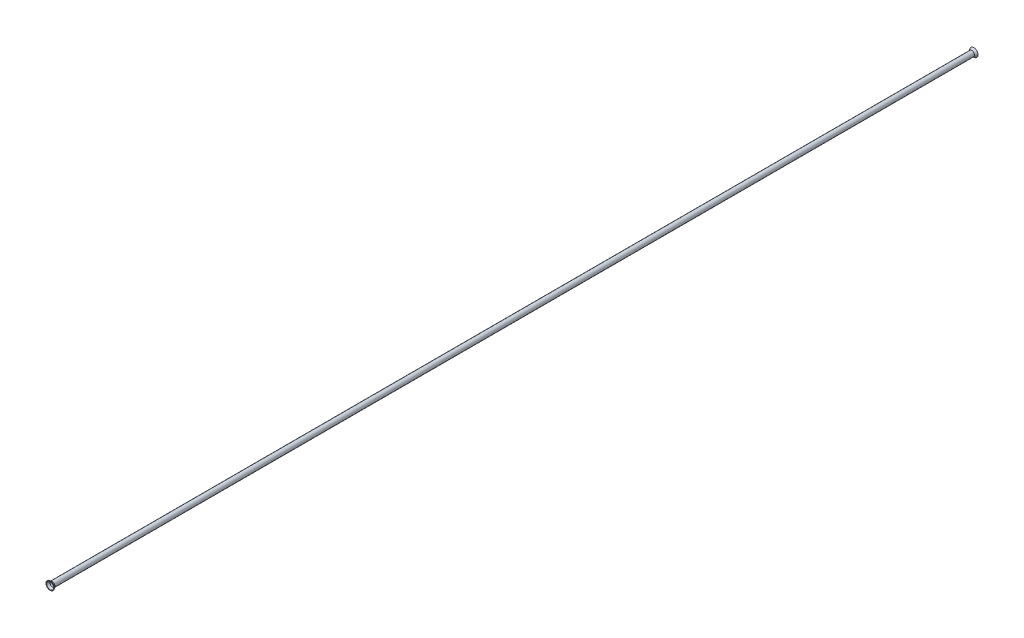
SolidWorks part; units mm, degrees
material "6061-T6 (SS)"
ref_plane "Front Plane" through (0, 0, 0) normal (0, 0, 1) x (1, 0, 0)
ref_plane "Top Plane" through (0, 0, 0) normal (0, 1, 0) x (1, 0, 0)
ref_plane "Right Plane" through (0, 0, 0) normal (1, 0, 0) x (0, 0, -1)
sketch "Sketch1" plane through (0, 0, 0) normal (0, 0, 1) x (1, 0, 0)
  circle A0 centre (0, 0) radius 2.3813
  circle A1 centre (0, 0) radius 1.8225
  dimension "D1" = 0.5588
  dimension "D2" = 4.7625
extrude "Boss-Extrude1" add sketch "Sketch1" along normal mid plane 817.5752
sketch "Sketch2" plane through (0, 0, 408.7876) normal (0, 0, 1) x (1, 0, 0)
  circle A0 centre (0, 0) radius 2.3813 construction
  circle A2 centre (0, 0) radius 2.3813
extrude "Boss-Extrude2" add sketch "Sketch2" along normal blind 1.778 draft 37 draft outward yes
sketch "Sketch3" plane through (0, 0, 408.7876) normal (0, 0, -1) x (-1, 0, 0)
  circle A0 centre (0, 0) radius 1.8225 construction
  circle A1 centre (0, 0) radius 1.8225
extrude "Cut-Extrude1" cut sketch "Sketch3" against normal through all draft 37 draft outward yes
mirror "Mirror1" about plane through (0, 0, 0) normal (0, 0, 1) of "Cut-Extrude1", "Boss-Extrude2"
